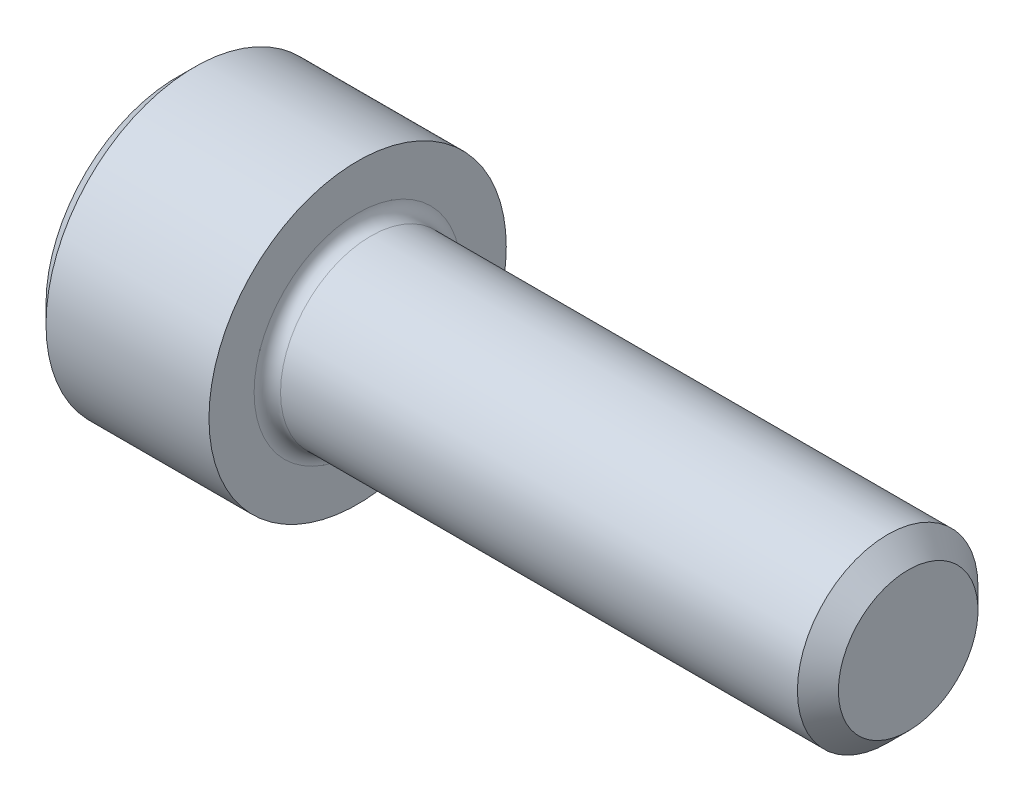
SolidWorks part; units mm, degrees
revolve "Base-Revolve" add sketch "BodySke"
sketch "BodySke" plane through (0, 0, 0) normal (0, 0, 1) x (1, 0, 0)
  line L0 (0, 0) -> (0, 3.0226)
  line L1 (0.4064, 3.429) -> (4.1656, 3.429)
  line L2 (4.1656, 3.429) -> (4.1656, 2.0828)
  line L3 (4.1656, 2.0828) -> (16.3932, 2.0828)
  line L4 (16.8656, 1.6104) -> (16.8656, 0)
  line L5 (16.8656, 0) -> (0, 0)
  line L6 (-31.75, 0) -> (127, 0) construction
  line L7 (0, 3.0226) -> (0.4064, 3.429)
  line L8 (16.8656, 1.6104) -> (16.3932, 2.0828)
  line L9 (0, -3.0226) -> (0.4064, -3.429) construction
  line L10 (16.8656, -1.6104) -> (16.3932, -2.0828) construction
  line L11 (4.9581, 9.525) -> (4.9581, 3.175) construction
  line L12 (4.1656, 9.525) -> (4.1656, 3.175) construction
  line L13 (-21.2344, 9.525) -> (-21.2344, 3.175) construction
  dimension "Diameter" = 4.1656
  dimension "Head_ht" = 4.1656
  dimension "Length" = 12.7
  dimension "Body_ch_ang" = 45
  dimension "Head_dia" = 6.858
  dimension "Head_ch_ang" = 45
  dimension "Head_side_ht" = 3.7592
  dimension "Minor_dia" = 3.2207
  dimension "Advance" = 0.7925
  dimension "Thread_nom" = 12.7
  dimension "Thread_length" = 38.1
cosmetic thread "ThreadCosmetic" [suppressed]
fillet "Fillet1" radius 0.3048 1 edges at (4.1656, 0, 2.0828)
ref_plane "Plane1" through (0, 0, 0) normal (0, 0, 1) x (1, 0, 0)
ref_plane "Plane2" through (0, 0, 0) normal (0, 1, 0) x (1, 0, 0)
ref_plane "Plane3" through (0, 0, 0) normal (1, 0, 0) x (0, 0, -1)
other "Configuration Table"
sketch "Sketch2" plane through (0, 0, 0) normal (0, 0, 1) x (1, 0, 0)
  line L0 (0, 1.778) -> (1.9558, 1.778)
  line L1 (1.9558, 1.778) -> (2.9823, 0)
  line L2 (-31.75, 0) -> (127, 0) construction
  line L3 (2.9823, 0) -> (0, 0)
  line L4 (0, 0) -> (0, 1.778)
  line L5 (0, 3.0226) -> (0, -3.0226) construction
  line L6 (0, 0) -> (47.625, 0) construction
  line L7 (4.1656, -3.429) -> (4.1656, 3.429) construction
  dimension "D1" = 1.778
  dimension "D2" = 60
revolve "Hex-PreBroach" cut sketch "Sketch2" angle 360 about L6
sketch "Sketch3" plane through (0, 0, 0) normal (-1, 0, 0) x (0, 0.5, 0.866)
  line L0 (1.0265, 1.778) -> (-1.0265, 1.778)
  line L1 (-1.0265, 1.778) -> (-2.0531, 0)
  line L2 (1.0265, 1.778) -> (2.0531, 0)
  line L3 (1.0265, -1.778) -> (2.0531, 0)
  line L4 (1.0265, -1.778) -> (-1.0265, -1.778)
  line L5 (-1.0265, -1.778) -> (-2.0531, 0)
  dimension "D1" = 1.778
  dimension "D2" = 1.778
  dimension "Hex_size" = 3.556
extrude "Hex" cut sketch "Sketch3" against normal blind 1.9558
sketch "Sketch4" plane through (0, 0, 0) normal (-1, 0, 0) x (0, 0, 1)
  line L0 (0, 0) -> (2.1971, 0)
  line L1 (0, 0) -> (6.1484, 3.5498) construction
  line L2 (0, 0) -> (1.0985, 1.9027)
  line L3 (1.8302, 0.5287) -> (2.0897, 0.6786)
  line L4 (1.373, 1.3206) -> (1.6325, 1.4704)
  arc A0 (1.8302, 0.5287) -> (1.373, 1.3206) centre (0, 0) ccw
  arc A1 (2.1971, 0) -> (2.0897, 0.6786) centre (0, 0) ccw
  arc A2 (1.0985, 1.9027) -> (1.6325, 1.4704) centre (0, 0) cw
  dimension "D1" = 30
  dimension "D2" = 60
  dimension "Spline_p_dim" = 0.9144
  dimension "D3" = 0.4572
extrude "Spline" [suppressed] cut sketch "Sketch4" against normal blind 1.9558
pattern_circular "CirPattern1" [suppressed] count 6 every 60
sketch "Sketch5" plane through (0, 0, 0) normal (0, 0, 1) x (1, 0, 0)
  line L0 (-31.75, 0) -> (127, 0) construction
  line L2 (0, 3.0226) -> (0, -3.0226) construction
  circle A0 centre (1.524, 0) radius 0.5905
  dimension "Drilled_hole_dia" = 1.1811
  dimension "Drilled_hole_loc" = 1.524
extrude "Hole" [suppressed] cut sketch "Sketch5" against normal through all and the other way through all
pattern_circular "Drilled-4" [suppressed] count 2 every 60
pattern_circular "Drilled-6" [suppressed] count 3 every 60
sketch "ThdSchSke" plane through (0, 0, 0) normal (0, 0, 1) x (1, 0, 0)
  line L0 (4.9581, -1.6104) -> (4.6273, -2.0828)
  line L1 (4.9581, -1.6104) -> (5.2889, -2.0828)
  line L2 (5.2889, -2.0828) -> (5.2889, -2.6035)
  line L3 (-3.175, 0) -> (5.1513, 0) construction
  line L5 (5.2889, -2.6035) -> (4.6273, -2.6035)
  line L6 (4.6273, -2.6035) -> (4.6273, -2.0828)
  line L7 (0, 3.0226) -> (0, -3.0226) construction
  dimension "Thread_minor" = 3.2207
  dimension "Diameter" = 4.1656
  dimension "Start" = 4.9581
revolve "ThreadSchematic" [suppressed] cut sketch "ThdSchSke" angle 360 about L3
pattern_linear "ThdSchPat" [suppressed]
equation "\"D2@Sketch3\" = \"Hex_size@Sketch3\" / 2"
equation "\"D1@Sketch3\" = \"Hex_size@Sketch3\" / 2"
equation "\"D1@Sketch2\" = \"Hex_size@Sketch3\" / 2"
equation "\"D3@Sketch4\" = \"Spline_p_dim@Sketch4\" / 2"
equation "\"Thread_minor@ThreadCosmetic\"  =  \"Minor_dia@BodySke\""
equation "\"D2@CirPattern1\" = 360 / \"Num_teeth@CirPattern1\""
equation "\"Wall_thickness@Sketch2\" = \"Head_ht@BodySke\" - \"Key_eng@Hex\""
equation "\"Thread_length@ThreadCosmetic\" = ((sgn( (\"Length@BodySke\" - \"Advance@BodySke\" ) - \"Thread_nom@BodySke\" )-1)*( (\"Length@BodySke\" - \"Advance@BodySke\" ) - \"Thread_nom@BodySke\" ))/-2+ \"Thread_nom@BodySke\""
equation "\"Thread_minor@ThdSchSke\" = \"Minor_dia@BodySke\""
equation "\"Diameter@ThdSchSke\" = \"Diameter@BodySke\""
equation "\"Overcut@ThdSchSke\" = \"Diameter@BodySke\" * 1.25"
equation "\"Start@ThdSchSke\" = \"Head_ht@BodySke\" + \"Length@BodySke\" - \"Thread_length@ThreadCosmetic\"  '---Non-countersunk---"
equation "\"Num_threads@ThdSchPat\" = int( \"Thread_length@ThreadCosmetic\" / \"Advance@BodySke\" + 0.999 )  + 1"
equation "\"Advance@ThdSchPat\" = \"Thread_length@ThreadCosmetic\" /  (\"Num_threads@ThdSchPat\" - 1) 'relax it"
equation "\"Num_threads@ThdSchPat\" = \"Num_threads@ThdSchPat\" - sgn( \"Num_threads@ThdSchPat\" - 1) '---chamfered tips only---"
